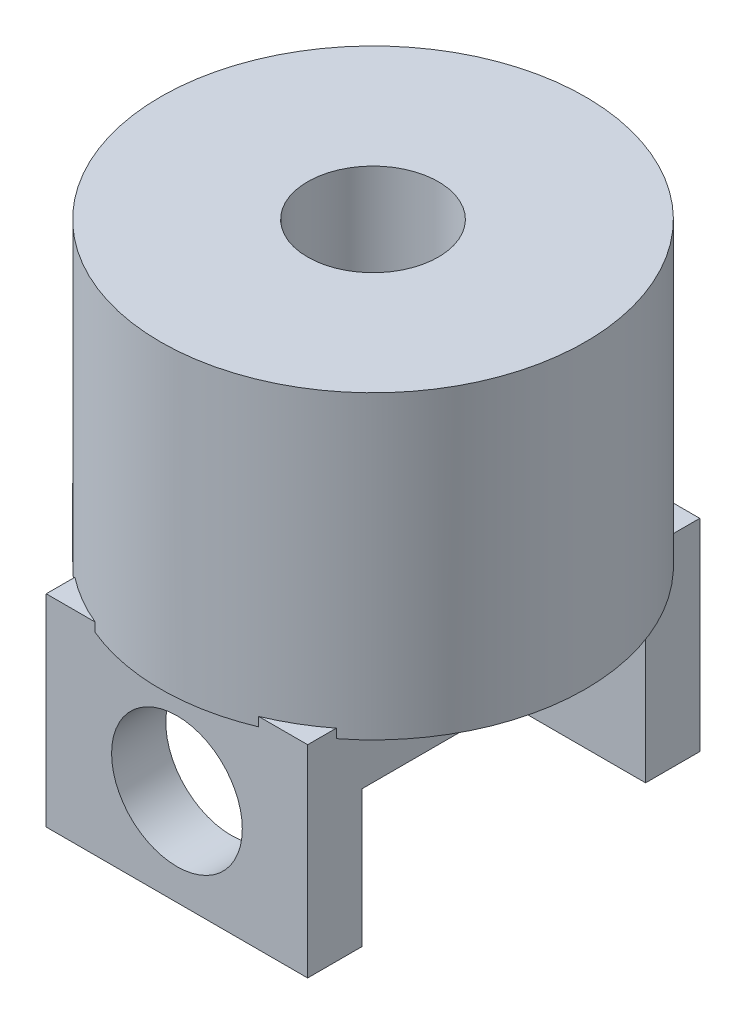
SolidWorks part; units mm, degrees
ref_plane "Front Plane" through (0, 0, 0) normal (0, 0, 1) x (1, 0, 0)
ref_plane "Top Plane" through (0, 0, 0) normal (0, 1, 0) x (1, 0, 0)
ref_plane "Right Plane" through (0, 0, 0) normal (1, 0, 0) x (0, 0, -1)
sketch "Sketch1" plane through (0, 0, 0) normal (0, 1, 0) x (1, 0, 0)
  circle A0 centre (0, 0) radius 32.5
  dimension "D1" = 65
extrude "Boss-Extrude1" add sketch "Sketch1" along normal blind 46
sketch "Sketch2" plane through (0, 46, 0) normal (0, 1, 0) x (1, 0, 0)
  circle A0 centre (0, 0) radius 10
  dimension "D1" = 20
extrude "Cut-Extrude1" cut sketch "Sketch2" against normal blind 40
sketch "Sketch3" plane through (0, 0, 0) normal (1, 0, 0) x (0, 0, -1)
  line L0 (0, -46) -> (0, 46) construction
  line L1 (10, 46) -> (-10, 46) construction
  line L2 (30, 1.3877) -> (-30, 1.3877)
  line L3 (-30, 1.3877) -> (-30, -29.526)
  line L4 (-30, -29.526) -> (-21.709, -29.526)
  line L5 (-21.709, -29.526) -> (-21.709, -8.6123)
  line L6 (-21.709, -8.6123) -> (21.709, -8.6123)
  line L7 (30, -29.526) -> (21.709, -29.526)
  line L8 (21.709, -29.526) -> (21.709, -8.6123)
  line L9 (30, 1.3877) -> (30, -29.526)
  point P6 (0, 0)
  point P16 (0, -8.6123)
  point P17 (0, 1.3877)
  dimension "D1" = 60
  dimension "D2" = 43.4179
  dimension "D3" = 20.9137
  dimension "D4" = 10
extrude "Boss-Extrude2" add sketch "Sketch3" along normal mid plane 40
sketch "Sketch4" plane through (0, 0, 0) normal (0, 0, 1) x (1, 0, 0)
  line L0 (0, 0) -> (0, -29.526) construction
  line L1 (20, -29.526) -> (-20, -29.526) construction
  circle A0 centre (0, -14.763) radius 10
  dimension "D1" = 20
extrude "Cut-Extrude2" cut sketch "Sketch4" against normal mid plane 84
